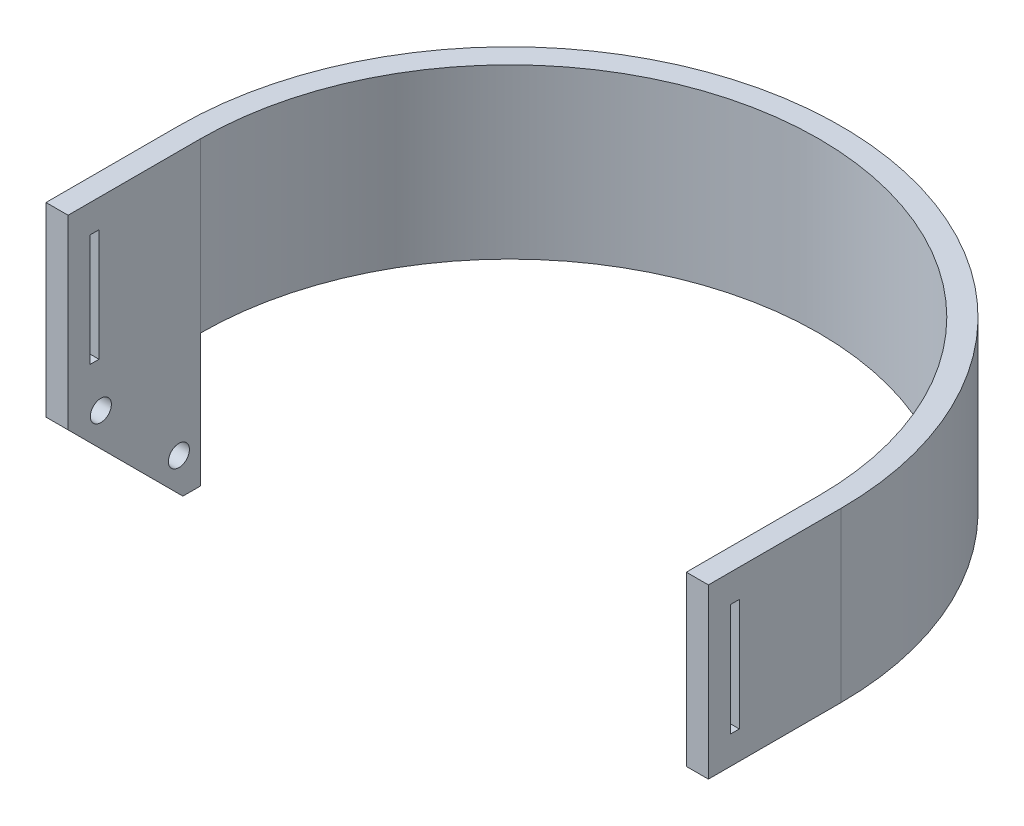
SolidWorks part; units mm, degrees
ref_plane "Front Plane" through (0, 0, 0) normal (0, 0, 1) x (1, 0, 0)
ref_plane "Top Plane" through (0, 0, 0) normal (0, 1, 0) x (1, 0, 0)
ref_plane "Right Plane" through (0, 0, 0) normal (1, 0, 0) x (0, 0, -1)
sketch "Sketch1" plane through (0, 0, 0) normal (0, 1, 0) x (1, 0, 0)
  line L0 (-75, 0) -> (75, 0)
  line L2 (-75, 0) -> (-70, 0)
  line L3 (-75, 0) -> (-75, -30)
  line L4 (-75, -30) -> (-70, -30)
  line L5 (-70, 0) -> (-70, -30)
  line L6 (70, 0) -> (75, 0)
  line L7 (70, 0) -> (70, -30)
  line L8 (70, -30) -> (75, -30)
  line L9 (75, 0) -> (75, -30)
  arc A0 (70, 0) -> (-70, 0) centre (0, 0) ccw
  arc A1 (75, 0) -> (-75, 0) centre (0, 0) ccw
  circle A2 centre (0, 0) radius 70 construction
  circle A3 centre (0, 0) radius 75 construction
  dimension "D1" = 140
  dimension "D3" = 30
  dimension "D2" = 5
extrude "Boss-Extrude1" add sketch "Sketch1" along normal blind 38.1 contours L5 L0 L3 L4 | L0 A1 A0 | L9 L0 L7 L8
sketch "Sketch2" plane through (75, 0, 0) normal (1, 0, 0) x (0, 0, -1)
  line L0 (0, 38.1) -> (-30, 38.1) construction
  line L1 (-25, 31.75) -> (-23, 31.75)
  line L2 (-25, 31.75) -> (-25, 6.35)
  line L3 (-25, 6.35) -> (-23, 6.35)
  line L4 (-23, 31.75) -> (-23, 6.35)
  line L5 (0, 0) -> (-30, 0) construction
  line L6 (-30, 38.1) -> (-30, 0) construction
  dimension "D1" = 6.35
  dimension "D2" = 6.35
  dimension "D3" = 5
  dimension "D4" = 2
extrude "Cut-Extrude1" cut sketch "Sketch2" against normal through all
sketch "Sketch3" plane through (75, 0, 0) normal (1, 0, 0) x (0, 0, -1)
  line L0 (-30, 0) -> (0, -30)
  line L1 (-30, 0) -> (0, 0)
  line L2 (-30, 0) -> (-30, -30)
  line L3 (-30, -30) -> (0, -30)
  line L4 (0, 0) -> (0, -30)
  line L5 (-30, 0) -> (0, -30)
  line L6 (-30, 0) -> (-26.4645, 3.5355)
  line L7 (0, -30) -> (3.5355, -26.4645)
  line L8 (-26.4645, 3.5355) -> (3.5355, -26.4645)
  line L9 (-28.2322, 1.7678) -> (1.7678, -28.2322)
  line L10 (-30, -4) -> (-4, -30)
  circle A0 centre (-22.5754, -3.8891) radius 2.3812
  circle A1 centre (-4.8977, -21.5668) radius 2.3813
  line M14 (-30, 0) -> (0, 0)
  dimension "D3" = 4.7625
  dimension "D6" = 4.7625
  dimension "D1" = 30
  dimension "D2" = 5
  dimension "D4" = 4
  dimension "D5" = 4
  dimension "D7" = 8
  dimension "D8" = 25
extrude "Boss-Extrude3" add sketch "Sketch3" against normal up to vertex (150 mm away) contours L2 L10 L3 L0 | A1 L9 A0 L0 L4 M14 | A1 L9 L4 L8 L1 A0 | L1 L8 L4
sketch "Sketch4" plane through (75, 0, 0) normal (1, 0, 0) x (0, 0, -1)
  line L1 (0, 0) -> (-32.7275, 0)
  line L2 (0, 0) -> (0, -37.1315)
  line L3 (0, -37.1315) -> (-32.7275, -37.1315)
  line L4 (-32.7275, 0) -> (-32.7275, -37.1315)
extrude "Cut-Extrude2" cut sketch "Sketch4" against normal up to vertex
